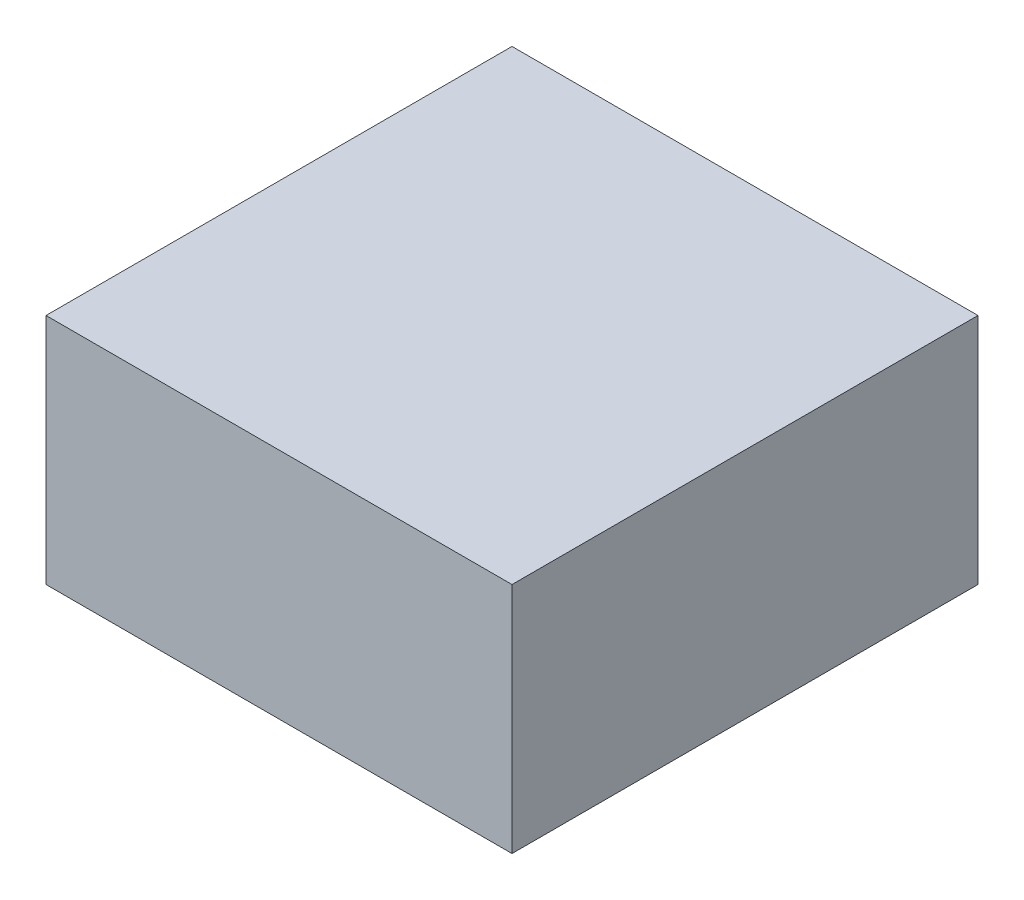
SolidWorks part; units mm, degrees
ref_plane "Front Plane" through (0, 0, 0) normal (0, 0, 1) x (1, 0, 0)
ref_plane "Top Plane" through (0, 0, 0) normal (0, 1, 0) x (1, 0, 0)
ref_plane "Right Plane" through (0, 0, 0) normal (1, 0, 0) x (0, 0, -1)
sketch "Sketch1" plane through (0, 0, 0) normal (0, 1, 0) x (1, 0, 0)
  line L1 (0, 0) -> (100, 0)
  line L2 (0, 0) -> (0, 100)
  line L3 (0, 100) -> (100, 100)
  line L4 (100, 0) -> (100, 100)
  dimension "D1" = 100
  dimension "D2" = 100
extrude "Boss-Extrude1" add sketch "Sketch1" along normal blind 50
